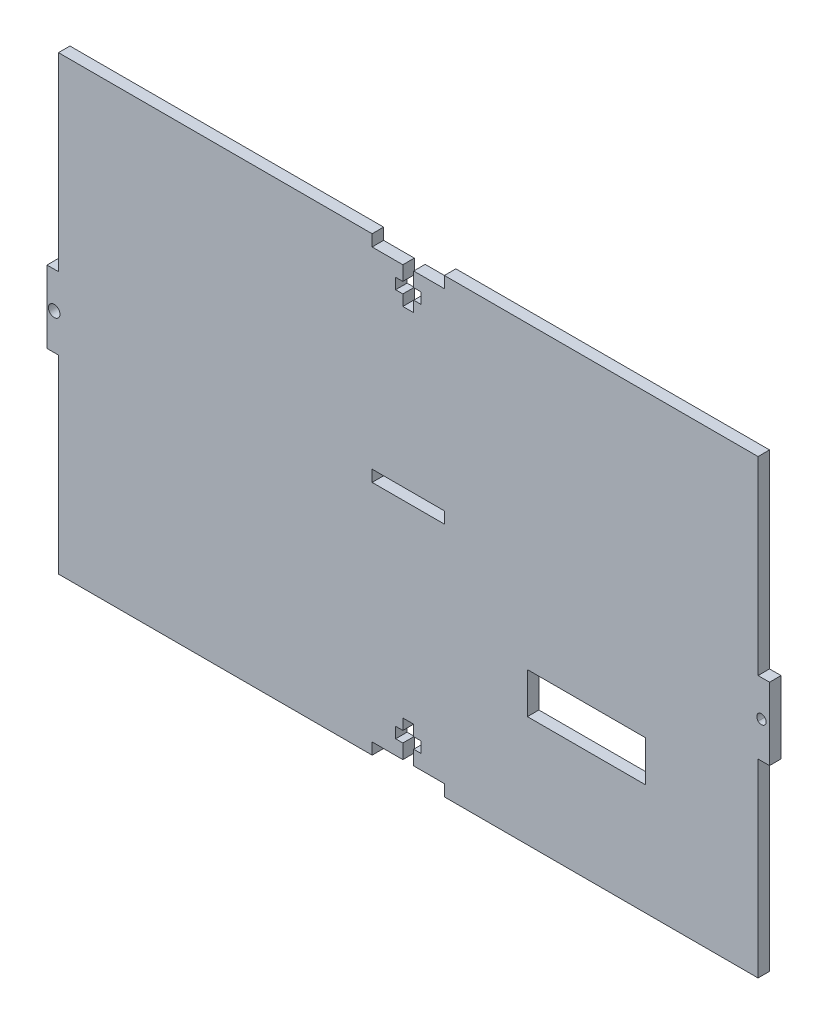
SolidWorks part; units mm, degrees
ref_plane "Front Plane" through (0, 0, 0) normal (0, 0, 1) x (1, 0, 0)
ref_plane "Top Plane" through (0, 0, 0) normal (0, 1, 0) x (1, 0, 0)
ref_plane "Right Plane" through (0, 0, 0) normal (1, 0, 0) x (0, 0, -1)
sketch "Sketch1" plane through (0, 0, 0) normal (0, 0, 1) x (1, 0, 0)
  line L1 (-100, 62.5) -> (100, 62.5)
  line L2 (-100, 62.5) -> (-100, -62.5)
  line L3 (-100, -62.5) -> (100, -62.5)
  line L4 (100, 62.5) -> (100, -62.5)
  line L5 (-100, 62.5) -> (100, -62.5) construction
  line L6 (-100, -62.5) -> (100, 62.5) construction
  point P0 (0, 0)
  dimension "D1" = 125
  dimension "D2" = 200
extrude "Boss-Extrude1" add sketch "Sketch1" along normal blind 3.18
sketch "Sketch2" plane through (0, 0, 3.18) normal (0, 0, 1) x (1, 0, 0)
  line L0 (0, 0) -> (100, 0) construction
  line L1 (-10, 62.5) -> (10, 62.5)
  line L2 (-10, 62.5) -> (-10, 59.32)
  line L3 (-10, 59.32) -> (-1.5, 59.32)
  line L4 (10, 62.5) -> (10, 59.32)
  line L5 (100, -62.5) -> (100, 62.5) construction
  line L6 (0, 0) -> (0, 62.5) construction
  line L7 (-1.5, 49.32) -> (1.5, 49.32)
  line L8 (-1.5, 49.32) -> (-1.5, 52.32)
  line L10 (1.5, 49.32) -> (1.5, 52.32)
  line L12 (100, 62.5) -> (-100, 62.5) construction
  line L13 (3.5, 55.32) -> (1.5, 55.32)
  line L14 (3.5, 55.32) -> (3.5, 52.32)
  line L15 (3.5, 52.32) -> (1.5, 52.32)
  line L16 (-3.5, 55.32) -> (-3.5, 52.32)
  line L17 (-10, -62.5) -> (-10, -59.32)
  line L18 (-10, -59.32) -> (-1.5, -59.32)
  line L19 (-1.5, -55.32) -> (-1.5, -59.32)
  line L20 (-1.5, -55.32) -> (-3.5, -55.32)
  line L21 (-3.5, -55.32) -> (-3.5, -52.32)
  line L22 (1.5, 59.32) -> (10, 59.32)
  line L23 (-1.5, 55.32) -> (-3.5, 55.32)
  line L24 (-1.5, -52.32) -> (-3.5, -52.32)
  line L25 (-1.5, -49.32) -> (-1.5, -52.32)
  line L26 (-1.5, -49.32) -> (1.5, -49.32)
  line L27 (-1.5, 52.32) -> (-3.5, 52.32)
  line L28 (1.5, -49.32) -> (1.5, -52.32)
  line L29 (-1.5, 55.32) -> (-1.5, 59.32)
  line L30 (1.5, 55.32) -> (1.5, 59.32)
  line L31 (3.5, -52.32) -> (1.5, -52.32)
  line L32 (3.5, -55.32) -> (3.5, -52.32)
  line L33 (3.5, -55.32) -> (1.5, -55.32)
  line L34 (1.5, -55.32) -> (1.5, -59.32)
  line L35 (1.5, -59.32) -> (10, -59.32)
  line L36 (10, -62.5) -> (10, -59.32)
  line L37 (-10, -62.5) -> (10, -62.5)
  line L38 (-100, 62.5) -> (-100, -62.5) construction
  line L39 (-100, 62.5) -> (-96.82, 62.5)
  line L40 (-100, 62.5) -> (-100, 9.875)
  line L41 (-100, 9.875) -> (-96.82, 9.875)
  line L42 (-96.82, 62.5) -> (-96.82, 9.875)
  line L43 (-100, -62.5) -> (-96.82, -62.5)
  line L44 (-100, -62.5) -> (-100, -9.875)
  line L45 (-100, -9.875) -> (-96.82, -9.875)
  line L46 (-96.82, -62.5) -> (-96.82, -9.875)
  line L47 (100, -9.875) -> (96.82, -9.875)
  line L48 (96.82, -62.5) -> (96.82, -9.875)
  line L49 (100, -62.5) -> (96.82, -62.5)
  line L50 (100, -62.5) -> (100, -9.875)
  line L51 (100, 9.875) -> (96.82, 9.875)
  line L52 (96.82, 62.5) -> (96.82, 9.875)
  line L53 (100, 62.5) -> (96.82, 62.5)
  line L54 (100, 62.5) -> (100, 9.875)
  circle A0 centre (-98, 0) radius 1.5
  circle A1 centre (98, 0) radius 1.5
  point P0 (0, 50.5662)
  point P5 (0, 32.0079)
  point P10 (15.4931, 34.4893)
  dimension "D11" = 3
  dimension "D12" = 2
  dimension "D1" = 20
  dimension "D2" = 19.75
  dimension "D3" = 4
  dimension "D4" = 3
  dimension "D5" = 3.18
  dimension "D6" = 7
  dimension "D7" = 3
  dimension "D8" = 3
  dimension "D9" = 3.18
  dimension "D10" = 3.18
extrude "Cut-Extrude1" cut sketch "Sketch2" against normal through all
sketch "Sketch6" plane through (0, 0, 0) normal (0, 0, -1) x (-1, 0, 0)
  line L0 (0, 0) -> (0, 73.5589) construction
  line L5 (10, 2.8888) -> (-10, 2.8888)
  line L6 (10, 2.8888) -> (10, 6.0688)
  line L7 (10, 6.0688) -> (-10, 6.0688)
  line L8 (-10, 2.8888) -> (-10, 6.0688)
  line L9 (10, 2.8888) -> (-10, 6.0688) construction
  line L10 (10, 6.0688) -> (-10, 2.8888) construction
  line L11 (-96.82, 62.5) -> (-10, 62.5) construction
  point P7 (0, 4.4788)
  point P16 (0, 0)
  dimension "D1" = 3.18
  dimension "D2" = 20
extrude "Cut-Extrude4" cut sketch "Sketch6" against normal blind 3.18
sketch "Sketch7" plane through (0, 0, 0) normal (0, 0, -1) x (-1, 0, 0)
  line L1 (-65.69, -20.4858) -> (-32.981, -20.4858)
  line L2 (-65.69, -20.4858) -> (-65.69, -31.7654)
  line L3 (-65.69, -31.7654) -> (-32.981, -31.7654)
  line L4 (-32.981, -20.4858) -> (-32.981, -31.7654)
extrude "Cut-Extrude5" cut sketch "Sketch7" against normal blind 3.18
sketch "Sketch8" plane through (0, 0, 0) normal (0, 0, -1) x (-1, 0, 0)
  line L1 (100, 9.875) -> (96.82, 9.875)
  line L2 (100, 9.875) -> (100, -9.875)
  line L3 (100, -9.875) -> (96.82, -9.875)
  line L4 (96.82, 9.875) -> (96.82, -9.875)
extrude "Cut-Extrude6" cut sketch "Sketch8" against normal through all
sketch "Sketch9" plane through (0, 0, 3.18) normal (0, 0, 1) x (1, 0, 0)
  line L1 (96.82, 9.875) -> (100, 9.875)
  line L2 (96.82, 9.875) -> (96.82, -9.875)
  line L3 (96.82, -9.875) -> (100, -9.875)
  line L4 (100, 9.875) -> (100, -9.875)
extrude "Cut-Extrude7" cut sketch "Sketch9" against normal through all
sketch "Sketch11" plane through (0, 0, 0) normal (0, 0, -1) x (-1, 0, 0)
  line L0 (-96.82, 62.5) -> (-96.82, 0.9261) construction
  line L1 (-96.82, 10) -> (-100, 10)
  line L2 (-96.82, 10) -> (-96.82, -10)
  line L3 (-96.82, -10) -> (-100, -10)
  line L4 (-100, 10) -> (-100, -10)
  dimension "D1" = 3.18
  dimension "D2" = 20
extrude "Boss-Extrude3" add sketch "Sketch11" against normal through all
sketch "Sketch12" plane through (0, 0, 0) normal (0, 0, -1) x (-1, 0, 0)
  arc A0 (-96.82, 0.9261) -> (-96.82, -0.9261) centre (-97.7461, 0) ccw
extrude "Cut-Extrude9" cut sketch "Sketch12" against normal through all and the other way through all
sketch "Sketch13" plane through (0, 0, 0) normal (0, 0, -1) x (-1, 0, 0)
  line L0 (96.82, -62.5) -> (96.82, -0.9261) construction
  line L1 (100, 10) -> (96.82, 10)
  line L2 (100, 10) -> (100, -10)
  line L3 (100, -10) -> (96.82, -10)
  line L4 (96.82, 10) -> (96.82, -10)
  dimension "3.18mm" = 3.18
  dimension "D2" = 20
extrude "Boss-Extrude4" add sketch "Sketch13" against normal through all
sketch "Sketch14" plane through (0, 0, 0) normal (0, 0, -1) x (-1, 0, 0)
  circle A3 centre (98, 0) radius 1.59
  arc A4 (96.82, 0.9261) -> (96.82, -0.9261) centre (98, 0) ccw construction
  dimension "D1" = 3.18
extrude "Cut-Extrude12" cut sketch "Sketch14" against normal blind 10
equation "\"sheet\"= 3.18mm"
equation "\"screwD\"= 2.94mm"
equation "\"tabW\"= 20mm"
equation "\"nut2\"= 6.5mm"
equation "\"3.18mm@Sketch13\" = \"sheet\""
equation "\"D2@Sketch13\"=\"tabW\""
